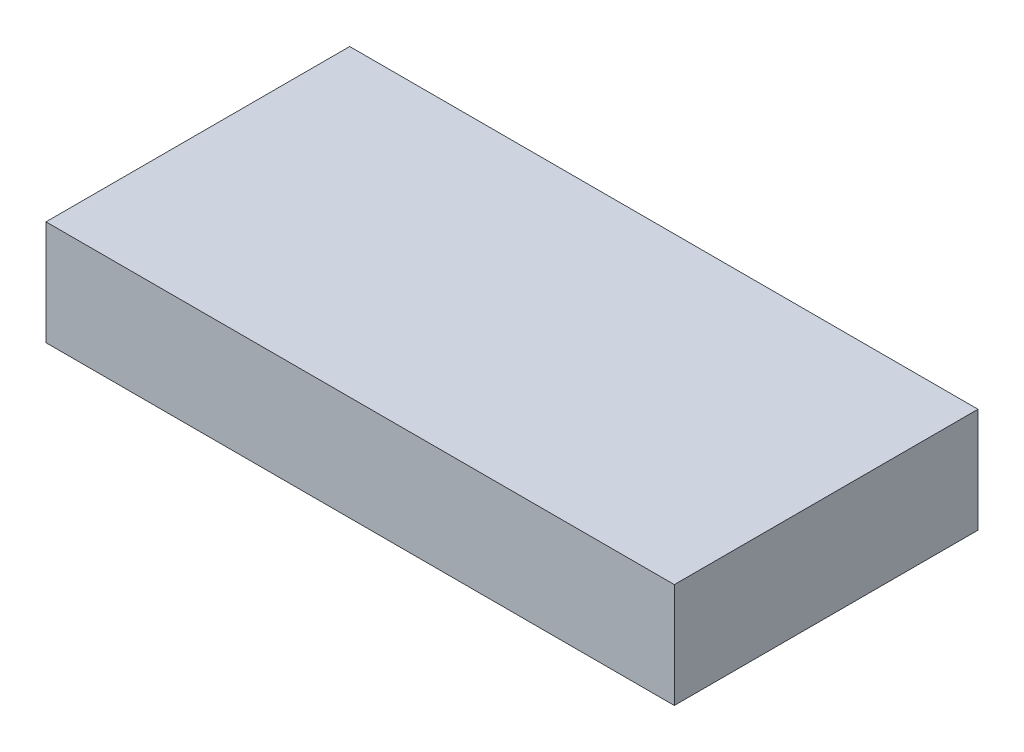
SolidWorks part; units mm, degrees
ref_plane "Front Plane" through (0, 0, 0) normal (0, 0, 1) x (1, 0, 0)
ref_plane "Top Plane" through (0, 0, 0) normal (0, 1, 0) x (1, 0, 0)
ref_plane "Right Plane" through (0, 0, 0) normal (1, 0, 0) x (0, 0, -1)
sketch "Sketch1" plane through (0, 0, 0) normal (0, 1, 0) x (1, 0, 0)
  line L1 (0, 0) -> (30, 0)
  line L2 (0, 0) -> (0, 14.5)
  line L3 (0, 14.5) -> (30, 14.5)
  line L4 (30, 0) -> (30, 14.5)
  dimension "D1" = 30
  dimension "D2" = 14.5
extrude "Boss-Extrude1" add sketch "Sketch1" along normal blind 5
